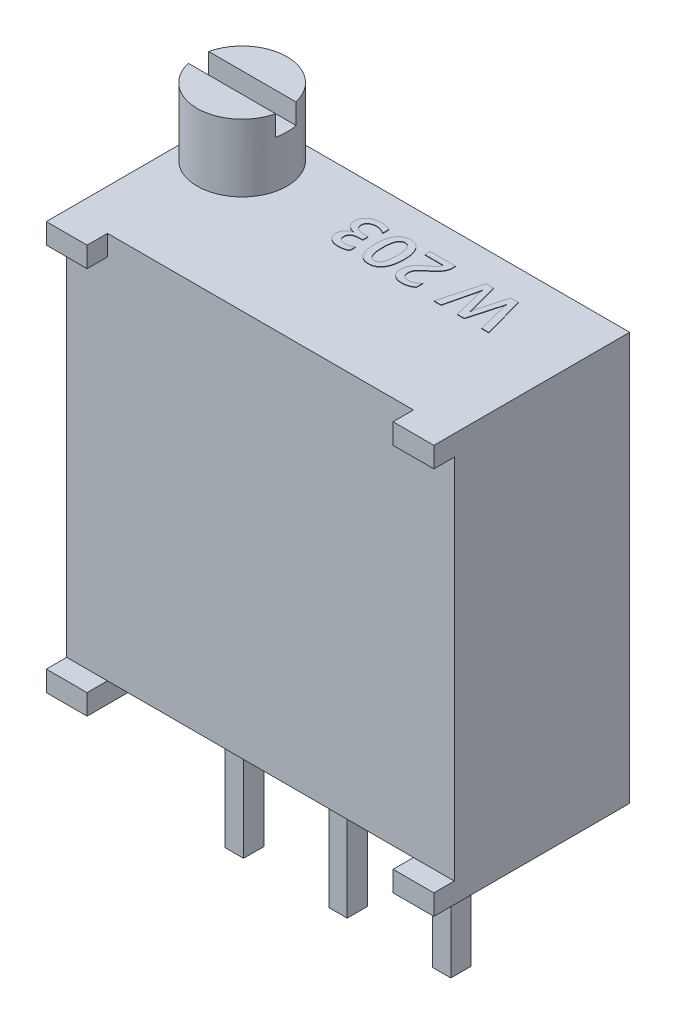
SolidWorks part; units mm, degrees
ref_plane "Front Plane" through (0, 0, 0) normal (0, 0, 1) x (1, 0, 0)
ref_plane "Top Plane" through (0, 0, 0) normal (0, 1, 0) x (1, 0, 0)
ref_plane "Right Plane" through (0, 0, 0) normal (1, 0, 0) x (0, 0, -1)
sketch "Sketch1" plane through (0, 0, 0) normal (0, 0, 1) x (1, 0, 0)
  line L0 (0, 0) -> (0, -4.75) construction
  line L1 (-3.75, -4.75) -> (3.75, -4.75)
  line L2 (-4.75, -4.75) -> (-4.75, 4.75)
  line L3 (-4.75, 4.75) -> (4.75, 4.75)
  line L4 (4.75, -4.75) -> (4.75, 4.75)
  line L5 (-4.75, -4.75) -> (4.75, 4.75) construction
  line L6 (-4.75, 4.75) -> (4.75, -4.75) construction
  line L7 (4.75, -4.75) -> (4.75, -5.25)
  line L8 (-4.75, -4.75) -> (-4.75, -5.25)
  line L9 (-4.75, -5.25) -> (-3.75, -5.25)
  line L10 (-3.75, -4.75) -> (-3.75, -5.25)
  line L11 (4.75, -5.25) -> (3.75, -5.25)
  line L12 (3.75, -4.75) -> (3.75, -5.25)
  point P0 (0, 0)
  dimension "D1" = 9.5
  dimension "D2" = 9.5
  dimension "D3" = 1
  dimension "D4" = 0.5
extrude "Boss-Extrude1" add sketch "Sketch1" along normal blind 4.3
sketch "Sketch2" plane through (0, 0, 4.3) normal (0, 0, 1) x (1, 0, 0)
  line L1 (-4.75, -5.25) -> (-3.75, -5.25)
  line L2 (-4.75, -5.25) -> (-4.75, -4.75)
  line L3 (-4.75, -4.75) -> (-3.75, -4.75)
  line L4 (-3.75, -5.25) -> (-3.75, -4.75)
  line L5 (4.75, -5.25) -> (3.75, -5.25)
  line L6 (4.75, -5.25) -> (4.75, -4.75)
  line L7 (4.75, -4.75) -> (3.75, -4.75)
  line L8 (3.75, -5.25) -> (3.75, -4.75)
  line L9 (-4.75, 4.75) -> (-3.75, 4.75)
  line L10 (-4.75, 4.75) -> (-4.75, 4.25)
  line L11 (-4.75, 4.25) -> (-3.75, 4.25)
  line L12 (-3.75, 4.75) -> (-3.75, 4.25)
  line L13 (4.75, 4.75) -> (3.75, 4.75)
  line L14 (4.75, 4.75) -> (4.75, 4.25)
  line L15 (4.75, 4.25) -> (3.75, 4.25)
  line L16 (3.75, 4.75) -> (3.75, 4.25)
  dimension "D1" = 0.5
  dimension "D2" = 0.5
extrude "Boss-Extrude2" add sketch "Sketch2" along normal blind 0.5
sketch "Sketch3" plane through (0, -4.75, 0) normal (0, -1, 0) x (1, 0, 0)
  line L0 (0, 2.15) -> (3.75, 2.15) construction
  line L1 (-0.225, 1.9) -> (0.225, 1.9)
  line L2 (-0.225, 1.9) -> (-0.225, 2.4)
  line L3 (-0.225, 2.4) -> (0.225, 2.4)
  line L4 (0.225, 1.9) -> (0.225, 2.4)
  line L5 (-0.225, 1.9) -> (0.225, 2.4) construction
  line L6 (-0.225, 2.4) -> (0.225, 1.9) construction
  line L7 (3.75, 4.3) -> (3.75, 0) construction
  line L8 (0, 0) -> (0, 2.15) construction
  line L9 (-3.75, 0) -> (3.75, 0) construction
  line L10 (2.315, 1.9) -> (2.765, 1.9)
  line L11 (2.315, 1.9) -> (2.315, 2.4)
  line L12 (2.315, 2.4) -> (2.765, 2.4)
  line L13 (2.765, 1.9) -> (2.765, 2.4)
  line L14 (2.315, 1.9) -> (2.765, 2.4) construction
  line L15 (2.315, 2.4) -> (2.765, 1.9) construction
  line L16 (-0.225, 1.9) -> (0.225, 1.9) [skipped]
  line L17 (-0.225, 1.9) -> (-0.225, 2.4) [skipped]
  line L18 (-0.225, 2.4) -> (0.225, 2.4) [skipped]
  line L19 (0.225, 1.9) -> (0.225, 2.4) [skipped]
  line L20 (-0.225, 1.9) -> (0.225, 2.4) construction
  line L21 (-0.225, 2.4) -> (0.225, 1.9) construction
  line L22 (-2.765, 1.9) -> (-2.315, 1.9)
  line L23 (-2.765, 1.9) -> (-2.765, 2.4)
  line L24 (-2.765, 2.4) -> (-2.315, 2.4)
  line L25 (-2.315, 1.9) -> (-2.315, 2.4)
  line L26 (-2.765, 1.9) -> (-2.315, 2.4) construction
  line L27 (-2.765, 2.4) -> (-2.315, 1.9) construction
  point P0 (0, 2.15)
  point P15 (2.54, 2.15)
  point P20 (0, 2.15)
  point P25 (-2.54, 2.15)
  dimension "D1" = 0.5
  dimension "D2" = 0.45
  dimension "D3" = 2
  dimension "D4" = 2
extrude "Boss-Extrude3" add sketch "Sketch3" along normal blind 4 separate body
sketch "Sketch4" plane through (0, 4.75, 0) normal (0, 1, 0) x (1, 0, 0)
  line L0 (4.75, 0) -> (-4.75, 0) construction
  line L1 (-4.75, -4.8) -> (-4.75, 0) construction
  circle A0 centre (-3.65, -1.1) radius 1.1
  dimension "D1" = 2.2
extrude "Boss-Extrude4" add sketch "Sketch4" along normal blind 1.65 separate body
sketch "Sketch5" plane through (0, 6.4, 0) normal (0, 1, 0) x (1, 0, 0)
  line L1 (-4.9, -1.35) -> (-2.4, -1.35)
  line L2 (-4.9, -1.35) -> (-4.9, -0.85)
  line L3 (-4.9, -0.85) -> (-2.4, -0.85)
  line L4 (-2.4, -1.35) -> (-2.4, -0.85)
  line L5 (-4.9, -1.35) -> (-2.4, -0.85) construction
  line L6 (-4.9, -0.85) -> (-2.4, -1.35) construction
  point P0 (-3.65, -1.1)
  dimension "D1" = 0.5
  dimension "D2" = 2.5
extrude "Cut-Extrude1" cut sketch "Sketch5" against normal blind 0.5
sketch "Sketch6" plane through (0, 4.75, 0) normal (0, 1, 0) x (1, 0, 0)
  line L0 (3.4447, -0.7408) -> (-1.349, -0.7408) construction
  text T0 "<b>W 203</b>" font "Yu Gothic UI" height 1
extrude "Boss-Extrude5" add sketch "Sketch6" along normal blind 0.01
sketch "Sketch7" plane through (0, 0, 0) normal (0, 0, -1) x (-1, 0, 0)
  line L0 (-3.0218, 0.8684) -> (3.3143, 0.8684) construction
  text T0 "<b>TRIMMER </b>\r\n<b>20k Ohm</b>" font "Century Gothic" height 1
extrude "Boss-Extrude6" add sketch "Sketch7" along normal blind 0.01
